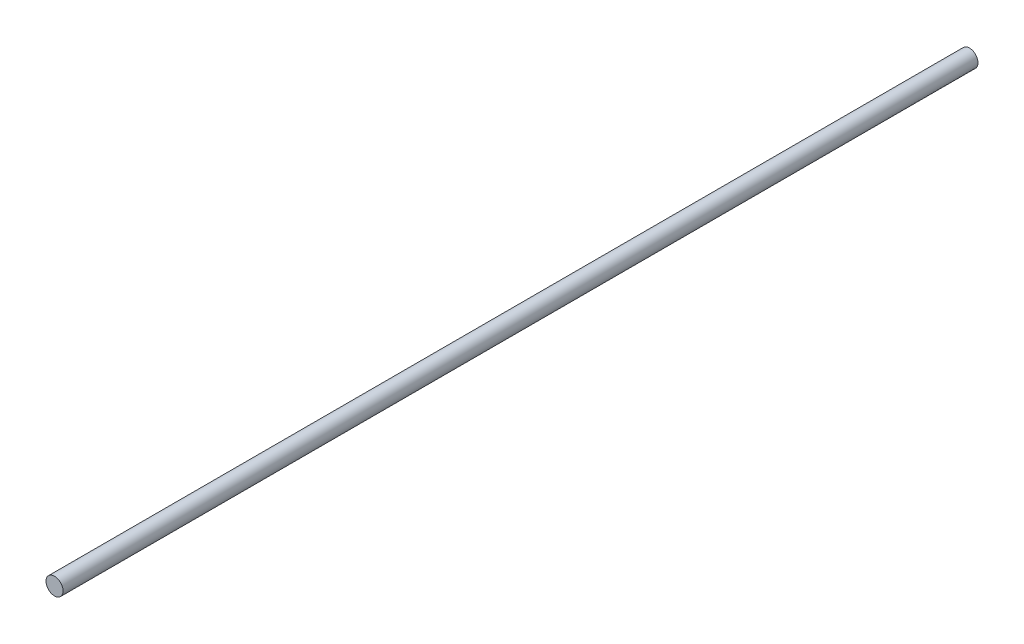
SolidWorks part; units mm, degrees
material "Plain Carbon Steel"
ref_plane "Front Plane" through (0, 0, 0) normal (0, 0, 1) x (1, 0, 0)
ref_plane "Top Plane" through (0, 0, 0) normal (0, 1, 0) x (1, 0, 0)
ref_plane "Right Plane" through (0, 0, 0) normal (1, 0, 0) x (0, 0, -1)
sketch "Sketch1" plane through (0, 0, 0) normal (0, 0, 1) x (1, 0, 0)
  circle A0 centre (0, 0) radius 4.7625
extrude "Boss-Extrude1" add sketch "Sketch1" against normal blind 510
